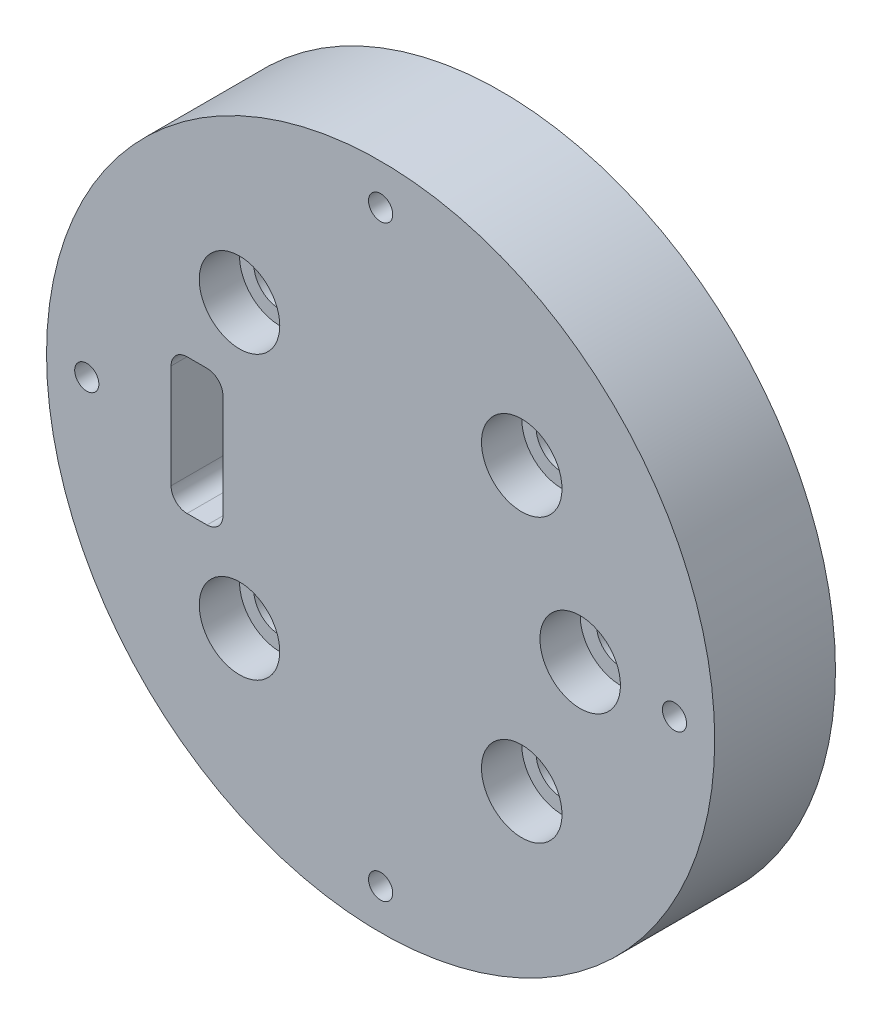
SolidWorks part; units mm, degrees
ref_plane "前视基准面" through (0, 0, 0) normal (0, 0, 1) x (1, 0, 0)
ref_plane "上视基准面" through (0, 0, 0) normal (0, 1, 0) x (1, 0, 0)
ref_plane "右视基准面" through (0, 0, 0) normal (1, 0, 0) x (0, 0, -1)
other "Configuration Table"
sketch "草图1" plane through (0, 0, 0) normal (0, 0, 1) x (1, 0, 0)
  line L0 (-21.5665, 8.4283) -> (-24.0454, 8.4283)
  line L1 (-26.0286, 6.4452) -> (-26.0286, -6.4452)
  line L2 (-24.0454, -8.4283) -> (-21.5665, -8.4283)
  line L3 (-19.5834, -6.4452) -> (-19.5834, 6.4452)
  line L4 (-19.5834, 6.4452) -> (-19.5834, -6.4452)
  arc A5 (20.7511, 17.5285) -> (14.306, 17.5285) centre (17.5285, 17.5285) ccw
  arc A6 (14.306, 17.5285) -> (20.7511, 17.5285) centre (17.5285, 17.5285) ccw
  arc A7 (27.7638, 0) -> (21.8144, 0) centre (24.7891, 0) ccw
  arc A8 (21.8144, 0) -> (27.7638, 0) centre (24.7891, 0) ccw
  arc A9 (20.7511, -17.5285) -> (14.306, -17.5285) centre (17.5285, -17.5285) ccw
  arc A10 (14.306, -17.5285) -> (20.7511, -17.5285) centre (17.5285, -17.5285) ccw
  arc A11 (-14.306, -17.5285) -> (-20.7511, -17.5285) centre (-17.5285, -17.5285) ccw
  arc A12 (-20.7511, -17.5285) -> (-14.306, -17.5285) centre (-17.5285, -17.5285) ccw
  arc A13 (-14.306, 17.5285) -> (-20.7511, 17.5285) centre (-17.5285, 17.5285) ccw
  arc A14 (-20.7511, 17.5285) -> (-14.306, 17.5285) centre (-17.5285, 17.5285) ccw
  arc A15 (-24.0454, 8.4283) -> (-26.0286, 6.4452) centre (-24.0454, 6.4452) ccw
  arc A16 (-26.0286, -6.4452) -> (-24.0454, -8.4283) centre (-24.0454, -6.4452) ccw
  arc A17 (-21.5665, -8.4283) -> (-19.5834, -6.4452) centre (-21.5665, -6.4452) ccw
  arc A18 (-19.5834, 6.4452) -> (-19.9854, 7.6422) centre (-21.5665, 6.4452) ccw
  arc A19 (-19.9854, 7.6422) -> (-21.5665, 8.4283) centre (-21.5665, 6.4452) ccw
  circle A20 centre (0, 0) radius 41.5
  dimension "D1" = 83
extrude "凸台-拉伸1" add sketch "草图1" along normal blind 5 and the other way blind 10
sketch "草图2" plane through (0, 0, 5) normal (0, 0, 1) x (1, 0, 0)
  arc A0 (-20.7511, 17.5285) -> (-14.306, 17.5285) centre (-17.5285, 17.5285) ccw construction
  arc A1 (-14.306, 17.5285) -> (-20.7511, 17.5285) centre (-17.5285, 17.5285) ccw construction
  arc A2 (20.7511, 17.5285) -> (14.306, 17.5285) centre (17.5285, 17.5285) ccw construction
  arc A3 (14.306, 17.5285) -> (20.7511, 17.5285) centre (17.5285, 17.5285) ccw construction
  arc A4 (21.8144, 0) -> (27.7638, 0) centre (24.7891, 0) ccw construction
  arc A5 (27.7638, 0) -> (21.8144, 0) centre (24.7891, 0) ccw construction
  arc A6 (14.306, -17.5285) -> (20.7511, -17.5285) centre (17.5285, -17.5285) ccw construction
  arc A7 (20.7511, -17.5285) -> (14.306, -17.5285) centre (17.5285, -17.5285) ccw construction
  arc A8 (-20.7511, -17.5285) -> (-14.306, -17.5285) centre (-17.5285, -17.5285) ccw construction
  arc A9 (-14.306, -17.5285) -> (-20.7511, -17.5285) centre (-17.5285, -17.5285) ccw construction
  arc A10 (-20.7511, 17.5285) -> (-14.306, 17.5285) centre (-17.5285, 17.5285) ccw
  arc A11 (-14.306, 17.5285) -> (-20.7511, 17.5285) centre (-17.5285, 17.5285) ccw
  arc A12 (20.7511, 17.5285) -> (14.306, 17.5285) centre (17.5285, 17.5285) ccw
  arc A13 (14.306, 17.5285) -> (20.7511, 17.5285) centre (17.5285, 17.5285) ccw
  arc A14 (21.8144, 0) -> (27.7638, 0) centre (24.7891, 0) ccw
  arc A15 (27.7638, 0) -> (21.8144, 0) centre (24.7891, 0) ccw
  arc A16 (14.306, -17.5285) -> (20.7511, -17.5285) centre (17.5285, -17.5285) ccw
  arc A17 (20.7511, -17.5285) -> (14.306, -17.5285) centre (17.5285, -17.5285) ccw
  arc A18 (-20.7511, -17.5285) -> (-14.306, -17.5285) centre (-17.5285, -17.5285) ccw
  arc A19 (-14.306, -17.5285) -> (-20.7511, -17.5285) centre (-17.5285, -17.5285) ccw
  circle A20 centre (-17.5285, 17.5285) radius 5
  circle A21 centre (17.5285, 17.5285) radius 5
  circle A22 centre (-17.5285, -17.5285) radius 5
  circle A23 centre (17.5285, -17.5285) radius 5
  circle A24 centre (24.7891, 0) radius 5
  dimension "D1" = 10
  dimension "D2" = 10
  dimension "D3" = 10
  dimension "D4" = 10
  dimension "D5" = 10
extrude "切除-拉伸1" cut sketch "草图2" against normal blind 5
sketch "草图4" plane through (0, 0, 5) normal (0, 0, 1) x (1, 0, 0)
  line L0 (-36.5, 0) -> (36.5, 0) construction
  line L1 (0, 0) -> (0, 36.5) construction
  line L2 (0, 36.5) -> (0, -36.5) construction
  circle A0 centre (-36.5, 0) radius 1.5
  circle A1 centre (0, -36.5) radius 1.5
  circle A2 centre (36.5, 0) radius 1.5
  circle A3 centre (0, 36.5) radius 1.5
  circle A4 centre (0, 0) radius 36.5 construction
  point P3 (0, -35.466)
  point P4 (-36.4832, 1.1081)
  point P9 (35.3817, 0)
  point P17 (0, 37.6563)
  point P18 (0, 35.466)
  point P19 (0, 35.466)
  dimension "D1" = 73
  dimension "D2" = 3
  dimension "D3" = 3
  dimension "D4" = 3
  dimension "D5" = 3
sketch "草图5" plane through (0, 0, -10) normal (0, 0, -1) x (-1, 0, 0)
  line L0 (0, 0) -> (0, 41.5) construction
  line L1 (0, 0) -> (41.5, 0) construction
  circle A0 centre (0, 0) radius 41.5 construction
extrude "切除-拉伸2" cut sketch "草图4" against normal through all
